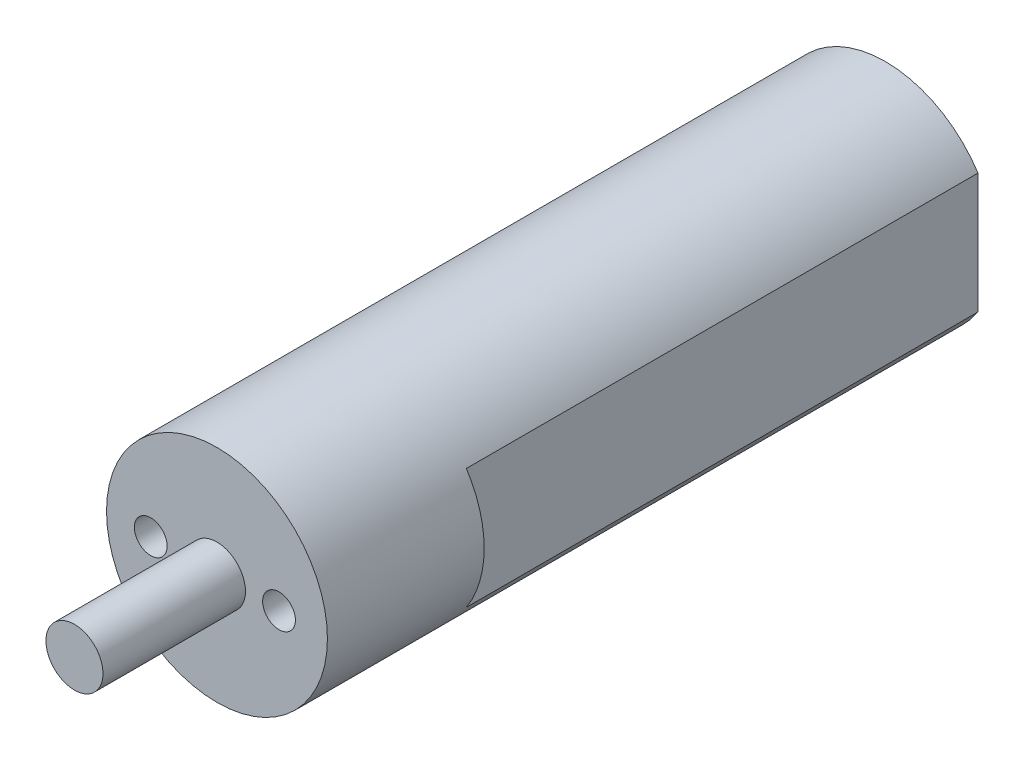
SolidWorks part; units mm, degrees
ref_plane "前视基准面" through (0, 0, 0) normal (0, 0, 1) x (1, 0, 0)
ref_plane "上视基准面" through (0, 0, 0) normal (0, 1, 0) x (1, 0, 0)
ref_plane "右视基准面" through (0, 0, 0) normal (1, 0, 0) x (0, 0, -1)
sketch "草图1" plane through (0, 0, 0) normal (0, 0, 1) x (1, 0, 0)
  line L0 (-10.6305, 0) -> (11.1609, 0) construction
  circle A0 centre (0, 0) radius 7.75
  circle A1 centre (4.3539, 0) radius 1.15
  circle A2 centre (-4.6461, 0) radius 1.15
  point P11 (-0.1461, 0)
  dimension "D1" = 2.3
  dimension "D2" = 15.5
  dimension "D4" = 9
  dimension "D3" = 2
extrude "凸台-拉伸1" add sketch "草图1" against normal blind 11
sketch "草图2" plane through (0, 0, -11) normal (0, 0, -1) x (-1, 0, 0)
  line L0 (6.5, 4.2205) -> (6.5, -4.2205)
  line L1 (0, 9.7439) -> (0, -10.7957) construction
  line L2 (-6.5, 4.2205) -> (-6.5, -4.2205)
  circle A0 centre (0, 0) radius 7.75 construction
  arc A1 (6.5, 4.2205) -> (-6.5, 4.2205) centre (0, 0) ccw
  arc A2 (-6.5, -4.2205) -> (6.5, -4.2205) centre (0, 0) ccw
  dimension "D1" = 6.5
extrude "凸台-拉伸2" add sketch "草图2" along normal blind 35.9
sketch "草图3" plane through (0, 0, 0) normal (0, 0, 1) x (1, 0, 0)
  circle A0 centre (0, 0) radius 2
  dimension "D1" = 4
extrude "凸台-拉伸3" add sketch "草图3" along normal blind 10
